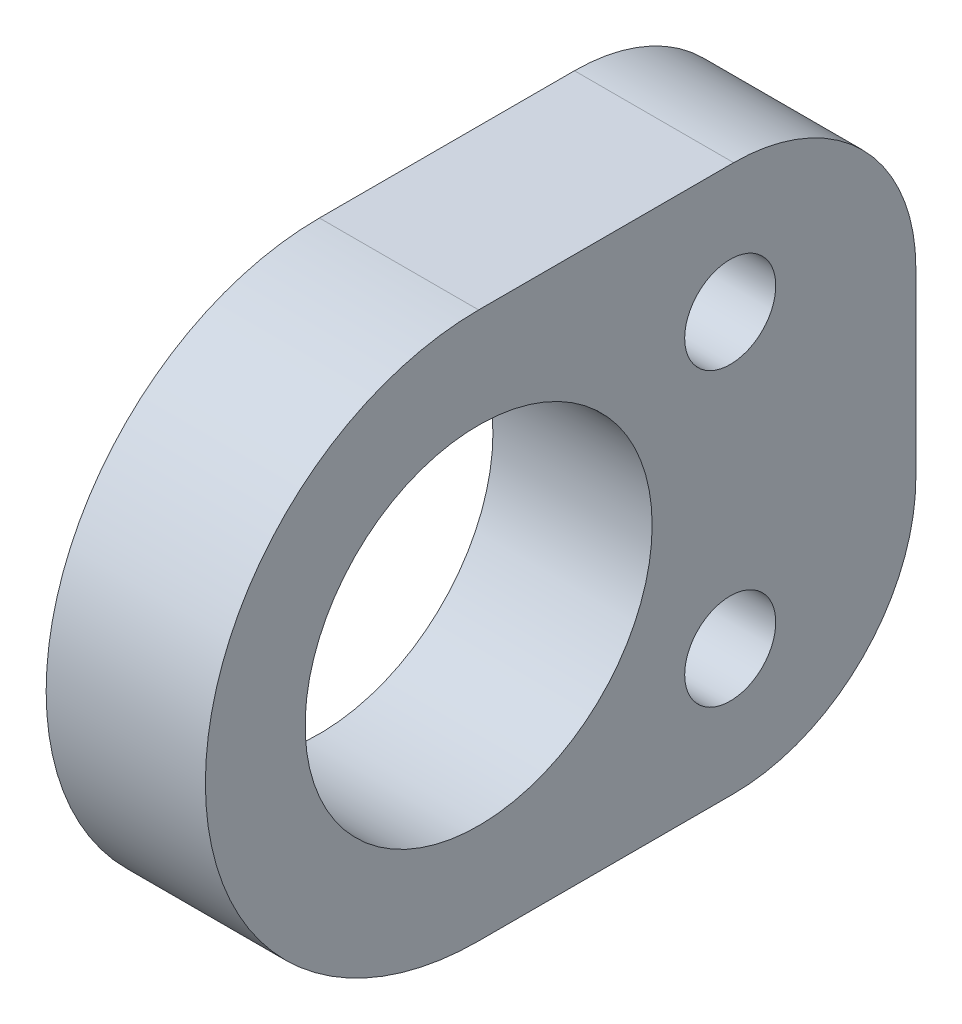
SolidWorks part; units mm, degrees
material "Plain Carbon Steel"
ref_plane "Front Plane" through (0, 0, 0) normal (0, 0, 1) x (1, 0, 0)
ref_plane "Top Plane" through (0, 0, 0) normal (0, 1, 0) x (1, 0, 0)
ref_plane "Right Plane" through (0, 0, 0) normal (1, 0, 0) x (0, 0, -1)
sketch "Sketch1" plane through (0, 0, 0) normal (1, 0, 0) x (0, 0, -1)
  line L0 (6.9051, 4) -> (6.9051, -4) construction
  line L1 (0, 7.5) -> (12, 7.5)
  line L2 (12, 7.5) -> (12, -7.5)
  line L3 (12, -7.5) -> (0, -7.5)
  arc A1 (6.9051, -4) -> (6.9051, 4) centre (0, 0) ccw construction
  circle A5 centre (0, 0) radius 4.7625
  arc A7 (0, 7.5) -> (0, -7.5) centre (0, 0) ccw
  point P21 (12, 0)
  dimension "D1" = 15
  dimension "D2" = 7.98
  dimension "D5" = 12
  dimension "D6" = 9.525
  dimension "D3" = 8
extrude "Boss-Extrude1" add sketch "Sketch1" along normal blind 4.37
fillet "Fillet1" radius 5 2 edges at (2.185, 7.5, -12) (2.185, -7.5, -12)
sketch "Sketch2" plane through (0, 0, 0) normal (-1, 0, 0) x (0, 0, 1)
  line L0 (-6.9051, 4) -> (-6.9051, -4) construction
  arc A0 (-6.9051, 4) -> (-6.9051, -4) centre (0, 0) ccw
  point P0 (-6.9051, 4)
  point P1 (-6.9051, -4)
  dimension "D1" = 7.98
hole_wizard "M3x0.5 Tapped Hole1" positions "Sketch2" profile "Sketch3" tap size "M3x0.5" standard "ANSI Metric" end condition through all
sketch "Sketch3" plane through (0, 4, -6.9051) normal (0, 1, 0) x (0, 0, 1)
  line L0 (0, 0) -> (0, 4.37)
  line L1 (0, 4.37) -> (1.25, 4.37)
  line L2 (1.25, 4.37) -> (1.25, 0)
  line L5 (1.25, 0) -> (0, 0)
  line L11 (0, -6.35) -> (0, 107.95) construction
  dimension "Thru Tap Drill Dia." = 2.5
  dimension "Thru Tap Drill Depth" = 4.37
cosmetic thread "Hole Thread1" parameters "D2"=3
cosmetic thread "Hole Thread2" parameters "D2"=3
